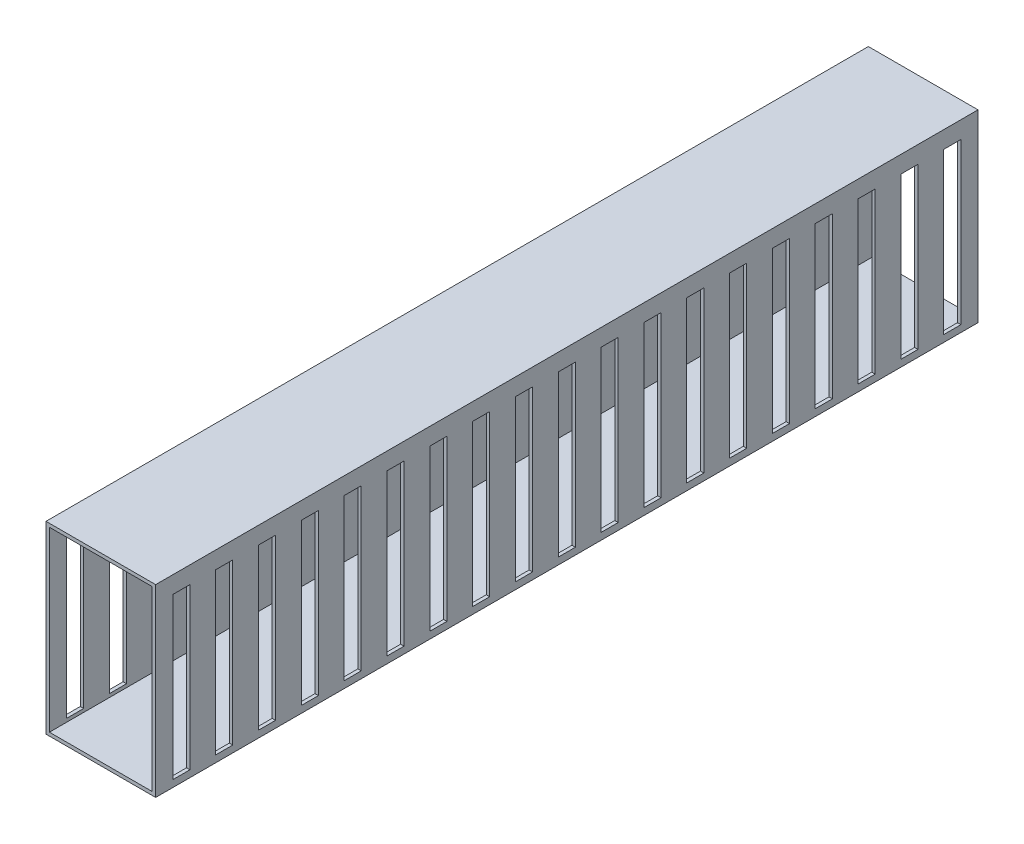
SolidWorks part; units mm, degrees
ref_plane "Plan de face" through (0, 0, 0) normal (0, 0, 1) x (1, 0, 0)
ref_plane "Plan de dessus" through (0, 0, 0) normal (0, 1, 0) x (1, 0, 0)
ref_plane "Plan de droite" through (0, 0, 0) normal (1, 0, 0) x (0, 0, -1)
sketch "Esquisse1" plane through (0, 0, 0) normal (0, 0, 1) x (1, 0, 0)
  line L0 (-12.0229, 36.1361) -> (-12.0229, -15.6639)
  line L1 (-13.0229, 37.1361) -> (18.9771, 37.1361)
  line L2 (-13.0229, 37.1361) -> (-13.0229, -16.6639)
  line L3 (-13.0229, -16.6639) -> (18.9771, -16.6639)
  line L4 (18.9771, 37.1361) -> (18.9771, -16.6639)
  line L5 (-12.0229, -15.6639) -> (17.9771, -15.6639)
  line L6 (17.9771, 36.1361) -> (17.9771, -15.6639)
  line L7 (-12.0229, 36.1361) -> (17.9771, 36.1361)
  dimension "D1" = 32
  dimension "D2" = 53.8
  dimension "D3" = 1
extrude "Boss.-Extru.1" add sketch "Esquisse1" along normal blind 240
sketch "Esquisse2" plane through (18.9771, 0, 0) normal (1, 0, 0) x (0, 0, -1)
  line L0 (-240, -16.6639) -> (0, -16.6639) construction
  line L1 (-5, -14.6639) -> (-10, -14.6639)
  line L2 (-5, -14.6639) -> (-5, 32.1361)
  line L3 (-5, 32.1361) -> (-10, 32.1361)
  line L4 (-10, -14.6639) -> (-10, 32.1361)
  line L5 (0, -16.6639) -> (0, 37.1361) construction
  line L6 (-240, 37.1361) -> (0, 37.1361) construction
  dimension "D1" = 2
  dimension "D2" = 5
  dimension "D3" = 5
  dimension "D4" = 5
extrude "Enlèv. mat.-Extru.1" cut sketch "Esquisse2" against normal up to surface (32 mm away) up to face at (-13.0229, 10.2361, 120)
pattern_linear "Répétition linéaire1" count 19 spacing 12.5 along (0, 0, 1) of "Enlèv. mat.-Extru.1"
